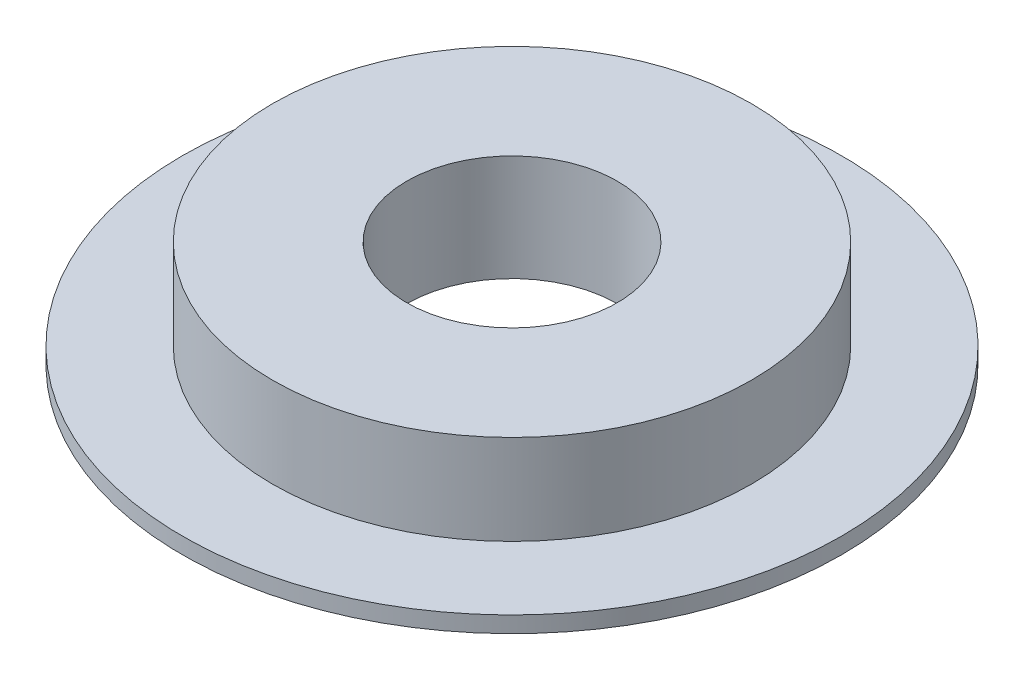
SolidWorks part; units mm, degrees
ref_plane "Alzado" through (0, 0, 0) normal (0, 0, 1) x (1, 0, 0)
ref_plane "Planta" through (0, 0, 0) normal (0, 1, 0) x (1, 0, 0)
ref_plane "Vista lateral" through (0, 0, 0) normal (1, 0, 0) x (0, 0, -1)
sketch "Croquis1" plane through (0, 0, 0) normal (0, 0, 1) x (1, 0, 0)
  line L0 (-29.4216, 13.9729) -> (-29.4216, -36.0271) construction
  line L1 (-29.4216, -11.0271) -> (-40.9216, -11.0271) construction
  line L2 (-41.1216, 8.9729) -> (-41.1216, -2.8271)
  line L3 (-29.4216, 8.9729) -> (-56.0216, 8.9729) construction
  line L4 (-41.1216, 8.9729) -> (-56.0216, 8.9729)
  line L5 (-56.0216, 8.9729) -> (-56.0216, -1.0271)
  line L6 (-56.0216, -1.0271) -> (-66.0216, -1.0271)
  line L7 (-66.0216, -1.0271) -> (-66.0216, -2.8271)
  line L8 (-66.0216, -2.8271) -> (-41.1216, -2.8271)
  dimension "D1" = 26.6
  dimension "D2" = 11.5
  dimension "D3" = 1.8
  dimension "D4" = 10
  dimension "D5" = 11.7
  dimension "D6" = 10
revolve "Revolución1" add sketch "Croquis1" angle 360 about L0
